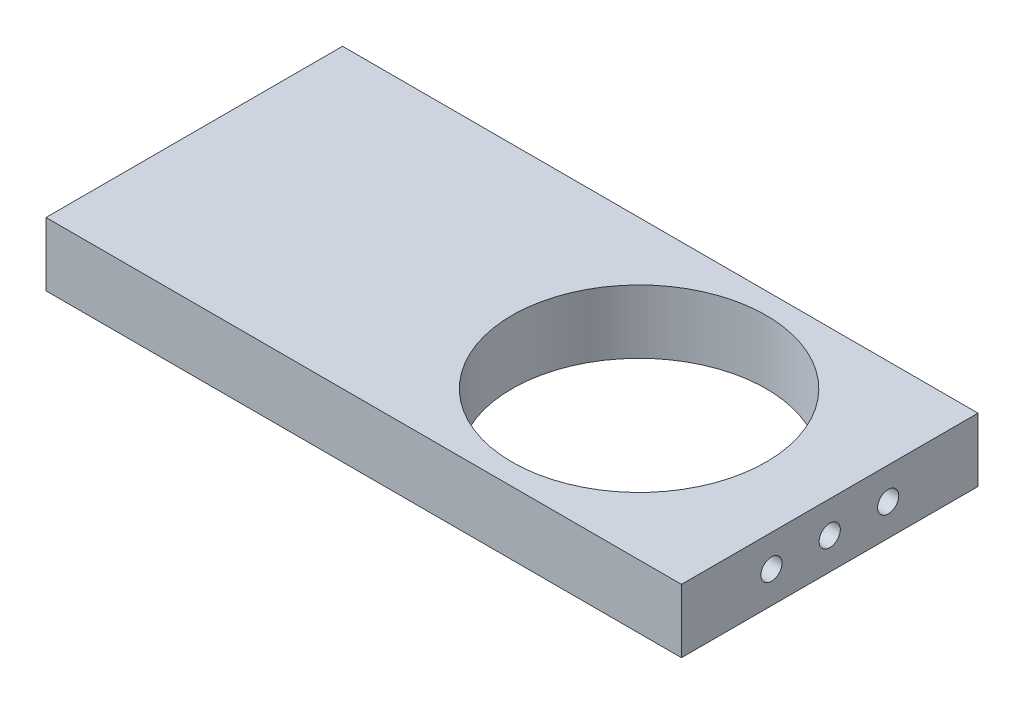
SolidWorks part; units mm, degrees
material "Pine"
ref_plane "Front Plane" through (0, 0, 0) normal (0, 0, 1) x (1, 0, 0)
ref_plane "Top Plane" through (0, 0, 0) normal (0, 1, 0) x (1, 0, 0)
ref_plane "Right Plane" through (0, 0, 0) normal (1, 0, 0) x (0, 0, -1)
sketch "Sketch1" plane through (0, 0, 0) normal (0, 1, 0) x (1, 0, 0)
  line L1 (-95.25, 44.45) -> (95.25, 44.45)
  line L2 (-95.25, 44.45) -> (-95.25, -44.45)
  line L3 (-95.25, -44.45) -> (95.25, -44.45)
  line L4 (95.25, 44.45) -> (95.25, -44.45)
  line L5 (-95.25, 44.45) -> (95.25, -44.45) construction
  line L6 (-95.25, -44.45) -> (95.25, 44.45) construction
  circle A0 centre (38.1, 0) radius 38.1
  point P0 (0, 0)
  dimension "D3" = 76.2
  dimension "D1" = 190.5
  dimension "D2" = 88.9
  dimension "D4" = 57.15
extrude "Boss-Extrude1" add sketch "Sketch1" along normal mid plane 19.05
sketch "Sketch2" plane through (95.25, 0, 0) normal (1, 0, 0) x (0, 0, -1)
  line L0 (-44.45, 9.525) -> (44.45, 9.525) construction
  line L1 (0, 0) -> (0, 9.525) construction
  circle A0 centre (0, 0) radius 3.175
  circle A1 centre (17.526, 0) radius 3.175
  circle A2 centre (-17.4625, 0) radius 3.175
  dimension "D1" = 6.35
  dimension "D2" = 17.4625
  dimension "D3" = 17.526
  dimension "D4" = 9.525
  dimension "D5" = 9.525
extrude "Cut-Extrude1" cut sketch "Sketch2" against normal blind 12.7
mirror "Mirror1" about plane through (0, 0, 0) normal (1, 0, 0) of "Cut-Extrude1"
